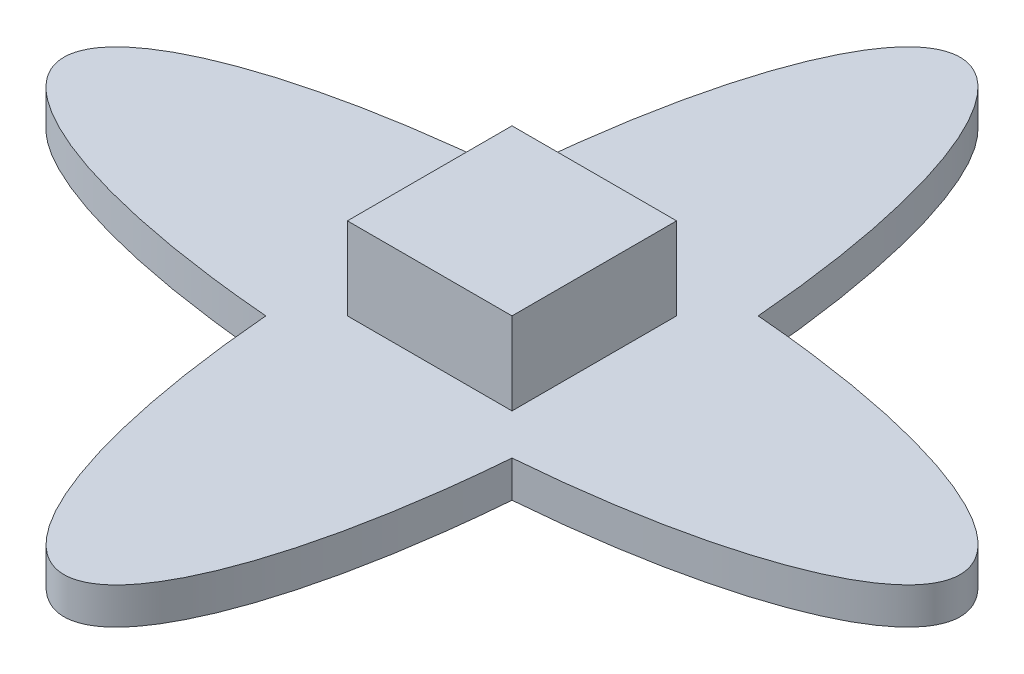
SolidWorks part; units mm, degrees
ref_plane "Front Plane" through (0, 0, 0) normal (0, 0, 1) x (1, 0, 0)
ref_plane "Top Plane" through (0, 0, 0) normal (0, 1, 0) x (1, 0, 0)
ref_plane "Right Plane" through (0, 0, 0) normal (1, 0, 0) x (0, 0, -1)
sketch "Sketch1" plane through (0, 0, 0) normal (0, 1, 0) x (1, 0, 0)
  ellipse E0 centre (0, 0) end of major axis (-24.5, 0) minor radius 7 (-6.7307, 6.7307) -> (-6.7307, -6.7307) ccw
  ellipse E1 centre (0, 0) end of major axis (0, -24.5) minor radius 7 (6.7307, 6.7307) -> (-6.7307, 6.7307) ccw
  ellipse E2 centre (0, 0) end of major axis (0, -24.5) minor radius 7 (-6.7307, -6.7307) -> (6.7307, -6.7307) ccw
  ellipse E3 centre (0, 0) end of major axis (-24.5, 0) minor radius 7 (6.7307, -6.7307) -> (6.7307, 6.7307) ccw
extrude "Boss-Extrude1" add sketch "Sketch1" along normal blind 2
sketch "Sketch2" plane through (0, 2, 0) normal (0, 1, 0) x (1, 0, 0)
  line L1 (-4.5, -4.5) -> (4.5, -4.5)
  line L2 (-4.5, -4.5) -> (-4.5, 4.5)
  line L3 (-4.5, 4.5) -> (4.5, 4.5)
  line L4 (4.5, -4.5) -> (4.5, 4.5)
  line L5 (-4.5, -4.5) -> (4.5, 4.5) construction
  line L6 (-4.5, 4.5) -> (4.5, -4.5) construction
  point P0 (0, 0)
  dimension "D1" = 9
  dimension "D2" = 9
extrude "Boss-Extrude2" add sketch "Sketch2" along normal blind 4.5
